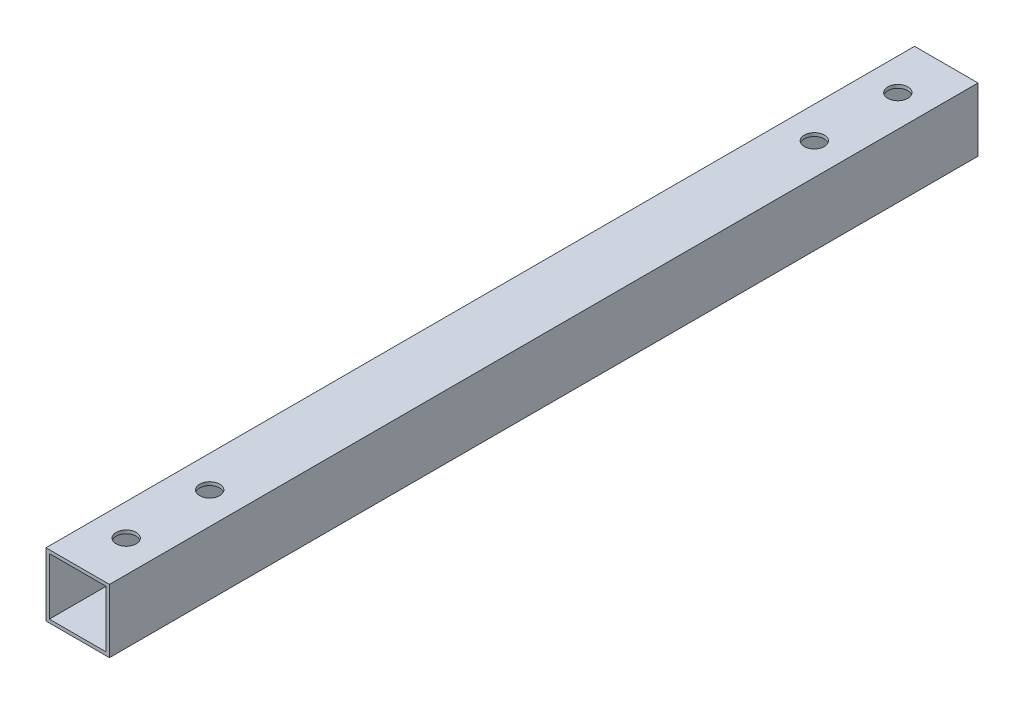
SolidWorks part; units mm, degrees
material "Gerais  - 6061-T6"
ref_plane "Plano frontal" through (0, 0, 0) normal (0, 0, 1) x (1, 0, 0)
ref_plane "Plano superior" through (0, 0, 0) normal (0, 1, 0) x (1, 0, 0)
ref_plane "Plano direito" through (0, 0, 0) normal (1, 0, 0) x (0, 0, -1)
sketch "Esboço1" plane through (0, 0, 0) normal (0, 0, 1) x (1, 0, 0)
  line L1 (-9.5, 9.5) -> (9.5, 9.5)
  line L2 (-9.5, 9.5) -> (-9.5, -9.5)
  line L3 (-9.5, -9.5) -> (9.5, -9.5)
  line L4 (9.5, 9.5) -> (9.5, -9.5)
  line L5 (-9.5, 9.5) -> (9.5, -9.5) construction
  line L6 (-9.5, -9.5) -> (9.5, 9.5) construction
  line L11 (-5.6574, 5.6574) -> (5.6574, -5.6574) construction
  line L12 (-5.6574, -5.6574) -> (5.6574, 5.6574) construction
  point P0 (0, 0)
  point P6 (0, 0)
  dimension "D1" = 19
extrude "Ressalto-extrusão1" add sketch "Esboço1" along normal blind 260
shell "Casca2" thickness 1
sketch "Esboço2" plane through (0, 9.5, 0) normal (0, 1, 0) x (1, 0, 0)
  circle A4 centre (0, -220.5) radius 3
  circle A5 centre (0, -245.5) radius 3
  circle A6 centre (0, -14.5) radius 3
  circle A7 centre (0, -39.5) radius 3
extrude "Corte-extrusão1" cut sketch "Esboço2" against normal through all
